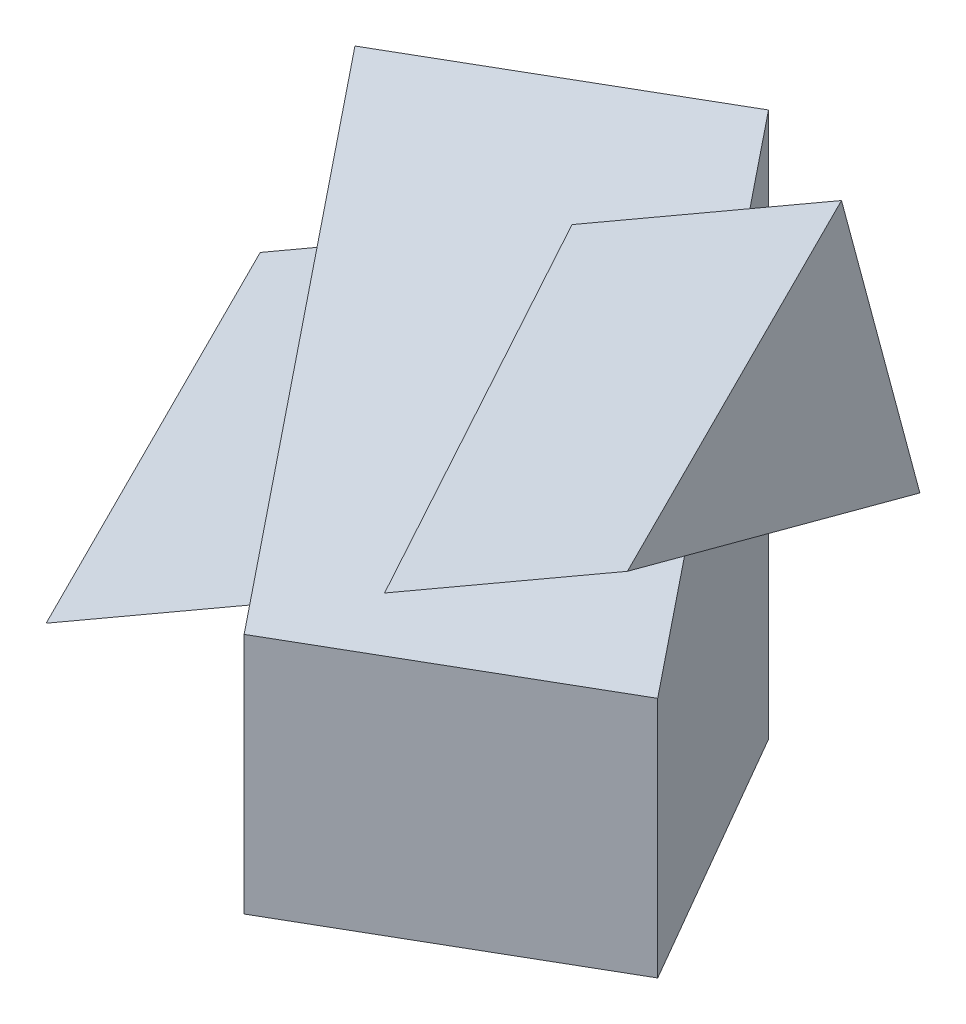
SolidWorks part; units mm, degrees
ref_plane "Front Plane" through (0, 0, 0) normal (0, 0, 1) x (1, 0, 0)
ref_plane "Top Plane" through (0, 0, 0) normal (0, 1, 0) x (1, 0, 0)
ref_plane "Right Plane" through (0, 0, 0) normal (1, 0, 0) x (0, 0, -1)
sketch "Sketch2" plane through (0, 0, 0) normal (0, 1, 0) x (1, 0, 0)
  line L0 (63.3013, 0) -> (20, -25)
  line L1 (63.3013, 0) -> (88.3013, -43.3013)
  line L2 (20, -25) -> (45, -68.3013)
  line L3 (88.3013, -43.3013) -> (45, -68.3013)
  line L4 (45, -68.3013) -> (-20.3672, -68.3013) construction
  dimension "D1" = 50
  dimension "D2" = 30
  dimension "D3" = 20
extrude "square prism" add sketch "Sketch2" along normal blind 90
sketch "Sketch3" plane through (4.1747, 0, -2.4103) normal (-0.866, 0, 0.5) x (0.5, 0, 0.866)
  line L0 (31.6506, 90) -> (81.6506, 90)
  line L1 (81.6506, 90) -> (81.6506, 40)
  line L2 (81.6506, 90) -> (81.6506, 0) construction
  line L3 (81.6506, 40) -> (31.6506, 90)
  line L4 (31.6506, 0) -> (81.6506, 0) construction
  dimension "D1" = 40
extrude "Cut on square prism" cut sketch "Sketch3" against normal through all
sketch "triangle" plane through (0, 0, 0) normal (1, 0, 0) x (0, 0, -1)
  line L0 (-7.7037, 0) -> (-20.6447, 48.2963)
  line L1 (-20.6447, 48.2963) -> (-56, 12.941)
  line L2 (-56, 12.941) -> (-7.7037, 0)
  line L3 (-7.7037, 0) -> (-7.7037, 35.9081) construction
  dimension "D1" = 50
  dimension "D2" = 15
  dimension "D3" = 56
ref_plane "Plane for swept path" through (0, 0, 56) normal (0, 0, 1) x (1, 0, 0)
sketch "path" plane through (0, 0, 56) normal (0, 0, 1) x (1, 0, 0)
  line L0 (0, 12.941) -> (96, 68.3666)
  line L1 (0, 0) -> (0, 35.9081) construction
  dimension "D1" = 96
  dimension "D2" = 60
sweep "Equilateral triangle prism" add profiles "triangle" path "path"
